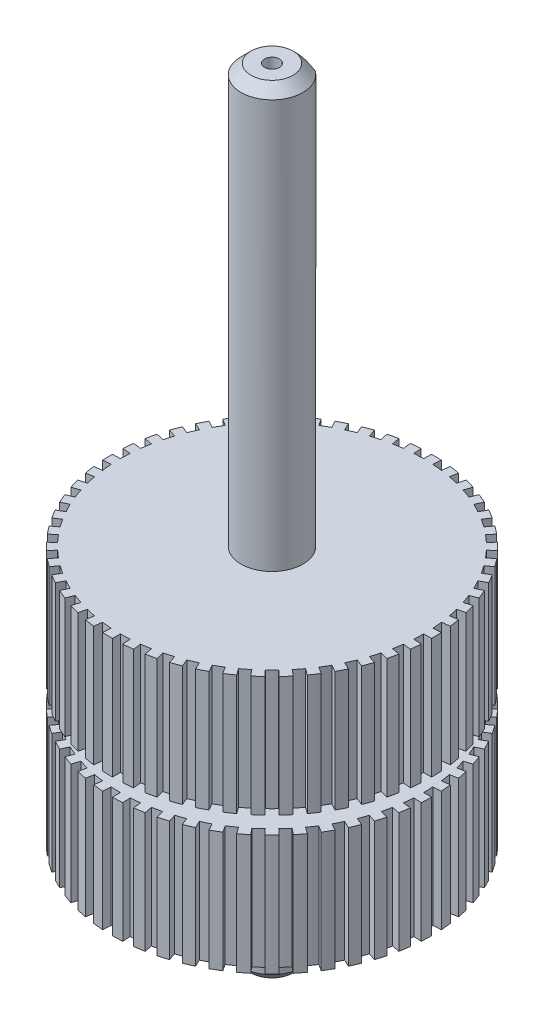
SolidWorks part; units mm, degrees
material "AISI 304"
ref_plane "Спереди" through (0, 0, 0) normal (0, 0, 1) x (1, 0, 0)
ref_plane "Сверху" through (0, 0, 0) normal (0, 1, 0) x (1, 0, 0)
ref_plane "Справа" through (0, 0, 0) normal (1, 0, 0) x (0, 0, -1)
sketch "Эскиз1" plane through (0, 0, 0) normal (0, 1, 0) x (1, 0, 0)
  circle A0 centre (0, 0) radius 12.89
  dimension "D1" = 25.78
extrude "Бобышка-Вытянуть1" add sketch "Эскиз1" along normal mid plane 20.8
sketch "Эскиз2" plane through (0, 10.4, 0) normal (0, 1, 0) x (1, 0, 0)
  circle A0 centre (0, 0) radius 2.5
  dimension "D1" = 5
extrude "Бобышка-Вытянуть2" add sketch "Эскиз2" along normal blind 33.8
sketch "Эскиз3" plane through (0, -10.4, 0) normal (0, -1, 0) x (1, 0, 0)
  circle A0 centre (0, 0) radius 2.5 construction
  circle A1 centre (0, 0) radius 2.5
extrude "Бобышка-Вытянуть3" add sketch "Эскиз3" along normal blind 8.2
sketch "Эскиз4" plane through (0, 10.4, 0) normal (0, 1, 0) x (1, 0, 0)
  line L0 (0, 0) -> (0, 12.89) construction
  line L1 (0, 0) -> (0.7692, 12.2258) construction
  line L2 (0, 0) -> (1.5353, 12.1534) construction
  line L3 (0.7692, 12.2258) -> (0.8094, 12.8646)
  line L4 (1.5353, 12.1534) -> (1.6155, 12.7884)
  circle A0 centre (0, 0) radius 12.89 construction
  arc A1 (1.6155, 12.7884) -> (0.8094, 12.8646) centre (0, 0) ccw
  arc A2 (0.7692, 12.2258) -> (1.5353, 12.1534) centre (0, 0) cw
  dimension "D3" = 12.25
  dimension "D1" = 3.6
  dimension "D2" = 3.6
sketch "Эскиз5" plane through (0, 0, 0) normal (0, 0, 1) x (1, 0, 0)
  line L0 (-12.89, 10.4) -> (-12.89, -10.4) construction
  line L1 (-9.89, -0.7) -> (-12.89, -0.7)
  line L2 (-9.89, -0.7) -> (-9.89, 0.7)
  line L3 (-9.89, 0.7) -> (-12.89, 0.7)
  line L4 (-12.89, -0.7) -> (-12.89, 0.7)
  line L5 (-9.89, -0.7) -> (-12.89, 0.7) construction
  line L6 (-9.89, 0.7) -> (-12.89, -0.7) construction
  line L7 (0, 0) -> (0, -10.4) construction
  line L8 (-2.5, -10.4) -> (2.5, -10.4) construction
  point P0 (-11.39, 0)
  dimension "D1" = 1.4
  dimension "D2" = 3
revolve "Вырез-Повернуть1" cut sketch "Эскиз5" angle 360 about L7
extrude "Вырез-Вытянуть1" cut sketch "Эскиз4" against normal up to surface (9.7 mm away) up to face at (0, 0.7, 12.89)
pattern_circular "Круговой массив1" count 50 over 360 about axis through (0, 0, 0) along (0, 1, 0) of "Вырез-Вытянуть1"
sketch "Эскиз6" plane through (0, -10.4, 0) normal (0, -1, 0) x (1, 0, 0)
  line L0 (0, 0) -> (0, -12.25) construction
  line L1 (0, 0) -> (0.7692, -12.2258) construction
  line L2 (0, -12.25) -> (0, -12.89)
  line L3 (0.7692, -12.2258) -> (0.8094, -12.8646)
  arc A0 (0, -12.25) -> (0.7692, -12.2258) centre (0, 0) ccw
  circle A1 centre (0, 0) radius 12.89 construction
  arc A2 (0, -12.89) -> (0.8094, -12.8646) centre (0, 0) ccw
  dimension "D2" = 12.25
  dimension "D1" = 3.6
extrude "Вырез-Вытянуть2" cut sketch "Эскиз6" against normal up to surface (9.7 mm away) up to face at (0, -0.7, 9.89)
pattern_circular "Круговой массив2" count 50 over 360 about axis through (0, 0, 0) along (0, 1, 0) of "Вырез-Вытянуть2"
sketch "Эскиз7" plane through (0, 44.2, 0) normal (0, 1, 0) x (1, 0, 0)
  circle A0 centre (0, 0) radius 0.6
  dimension "D1" = 1.2
extrude "Вырез-Вытянуть3" cut sketch "Эскиз7" against normal blind 4
sketch "Эскиз8" plane through (0, -18.6, 0) normal (0, -1, 0) x (1, 0, 0)
  circle A1 centre (0, 0) radius 0.6
  circle A2 centre (0, 0) radius 0.6
  dimension "D1" = 0
extrude "Вырез-Вытянуть4" cut sketch "Эскиз8" against normal blind 4
chamfer "Фаска1" distance 0.8 angle 45 2 edges at (0, 44.2, 2.5) (0, -18.6, -2.5)
sketch "Эскиз9" plane through (0, 44.2, 0) normal (0, 1, 0) x (1, 0, 0)
  line L0 (-1.5, 2) -> (1.5, 2)
  line L1 (0, 2) -> (0, 0) construction
  line L2 (0, 0) -> (0, -2.5) construction
  circle A0 centre (0, 0) radius 2.5 construction
  arc A1 (1.5, 2) -> (-1.5, 2) centre (0, 0) ccw
  dimension "D1" = 4.5
extrude "Вырез-Вытянуть5" cut sketch "Эскиз9" against normal blind 18
